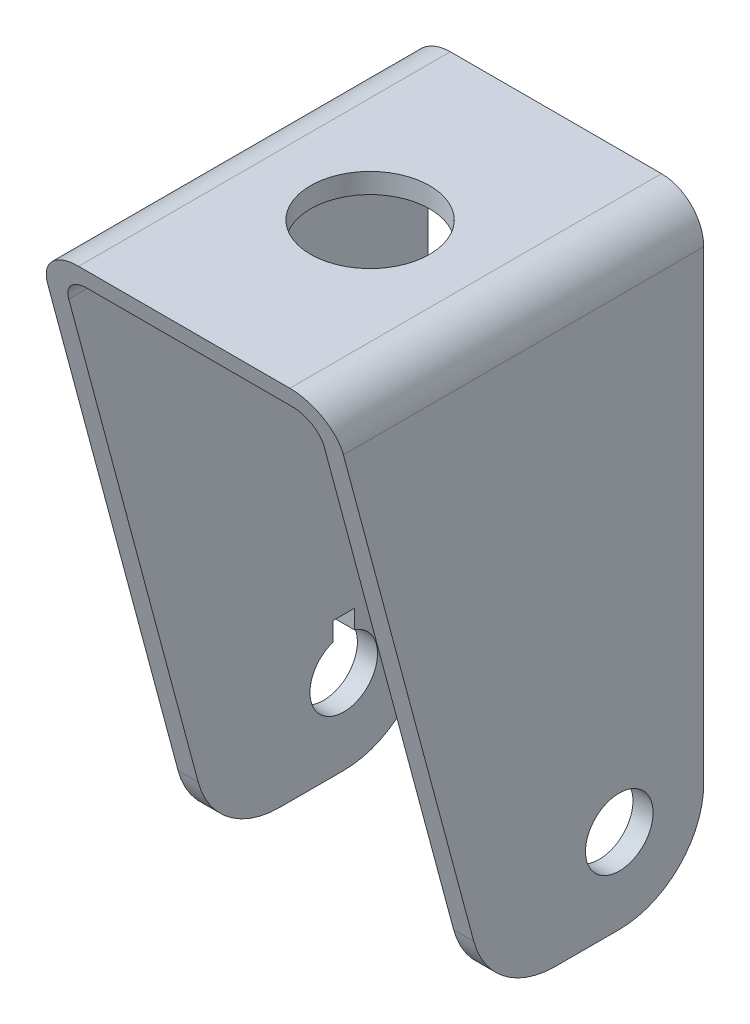
SolidWorks part; units mm, degrees
material "AISI 1020 Steel, Cold Rolled"
ref_plane "Front" through (0, 0, 0) normal (0, 0, 1) x (1, 0, 0)
ref_plane "Top" through (0, 0, 0) normal (0, 1, 0) x (1, 0, 0)
ref_plane "Right" through (0, 0, 0) normal (1, 0, 0) x (0, 0, -1)
sketch "Sketch1" plane through (0, 0, 0) normal (0, 0, 1) x (1, 0, 0)
  line L0 (0, 72.2359) -> (0, -78.3494) construction
  line L1 (-92.5661, 0) -> (110.6824, 0) construction
  line L2 (0, 0) -> (12.5, 0)
  line L3 (17.5, -5) -> (17.5, -70)
  line L4 (17.5, -70) -> (15.12, -70)
  line L5 (15.12, -70) -> (15.12, -5.38)
  line L6 (12.12, -2.38) -> (0, -2.38)
  line L7 (0, -2.38) -> (0, 0)
  arc A0 (15.12, -5.38) -> (12.12, -2.38) centre (12.12, -5.38) ccw
  arc A1 (12.5, 0) -> (17.5, -5) centre (12.5, -5) cw
  point P13 (15.12, -2.38)
  point P16 (17.5, 0)
  dimension "D5" = 3
  dimension "D6" = 5
  dimension "D1" = 35
  dimension "D2" = 70
  dimension "D3" = 2.38
  dimension "D4" = 2.38
extrude "Boss-Extrude1" add sketch "Sketch1" along normal mid plane 44
sketch "Sketch3" plane through (17.5, 0, 0) normal (1, 0, 0) x (0, 0, -1)
  line L0 (-22, 0) -> (-22, -70)
  line L1 (-22, -70) -> (-3.2436, -70)
  line L2 (-22, -70) -> (22, -70) construction
  line L3 (-3.2436, -70) -> (-22, 0)
  dimension "D1" = 75
extrude "Cut-Extrude1" cut sketch "Sketch3" against normal through all
sketch "Sketch4" plane through (17.5, 0, 0) normal (1, 0, 0) x (0, 0, -1)
  line L0 (12, -38.2232) -> (12, -81.3465) construction
  line L1 (-21.1216, -60) -> (38.2073, -60) construction
  line L2 (22, -70) -> (22, -5) construction
  line L3 (-3.2436, -70) -> (22, -70) construction
  circle A0 centre (12, -60) radius 4
  dimension "D3" = 8
  dimension "D1" = 10
  dimension "D2" = 10
extrude "Cut-Extrude2" cut sketch "Sketch4" against normal through all
fillet "Fillet2" radius 10 1 edges at (16.31, -70, -22)
fillet "Fillet3" radius 10 1 edges at (16.31, -70, 3.2436)
mirror "Mirror1" about plane through (0, 0, 0) normal (1, 0, 0) of bodies 103
sketch "Sketch5" plane through (0, 0, 0) normal (0, 1, 0) x (1, 0, 0)
  circle A0 centre (0, 0) radius 7.05
  dimension "D1" = 14.1
extrude "Cut-Extrude3" cut sketch "Sketch5" against normal through all
sketch "Sketch7" plane through (-17.5, 0, 0) normal (-1, 0, 0) x (0, 0, 1)
  line L0 (-12, -52.5295) -> (-12, -74.2918) construction
  line L1 (-24.9582, -60) -> (7.7142, -60) construction
  line L2 (-13.25, -54) -> (-10.75, -54)
  line L3 (-10.75, -54) -> (-10.75, -56.2003)
  line L4 (-13.25, -54) -> (-13.25, -56.2003)
  line L5 (-10.75, -56.2003) -> (-10.75, -56.3321)
  line L6 (-13.25, -56.2003) -> (-13.25, -56.3321)
  line L7 (-13.25, -56.3321) -> (-10.75, -56.3321)
  circle A0 centre (-12, -60) radius 4 construction
  point P12 (-12, -54)
  dimension "D1" = 2.5
  dimension "D2" = 6
extrude "Cut-Extrude6" cut sketch "Sketch7" against normal up to next
